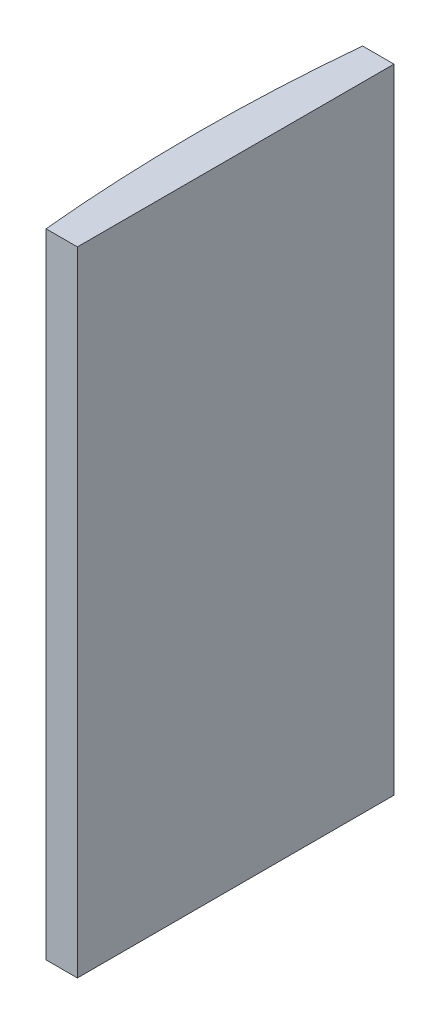
SolidWorks part; units mm, degrees
ref_plane "前视基准面" through (0, 0, 0) normal (0, 0, 1) x (1, 0, 0)
ref_plane "上视基准面" through (0, 0, 0) normal (0, 1, 0) x (1, 0, 0)
ref_plane "右视基准面" through (0, 0, 0) normal (1, 0, 0) x (0, 0, -1)
sketch "草图1" plane through (0, 0, 0) normal (0, 1, 0) x (1, 0, 0)
  line L0 (10.7432, 0) -> (-607.0701, 0) construction
  line L1 (-150.0178, 15) -> (-147.0448, 15)
  line L2 (-150.0178, -15) -> (-147.0448, -15)
  line L3 (-147.0448, 15) -> (-147.0448, -15)
  arc A0 (-150.0178, 15) -> (-150.0178, -15) centre (4.3552, 0) ccw
  point P19 (-150.7448, 0)
  point P20 (-147.0448, 0)
  dimension "D2" = 15
  dimension "D3" = 155.1
  dimension "D4" = 3.7
  dimension "D1" = 15
extrude "凸台-拉伸1" add sketch "草图1" along normal blind 60
